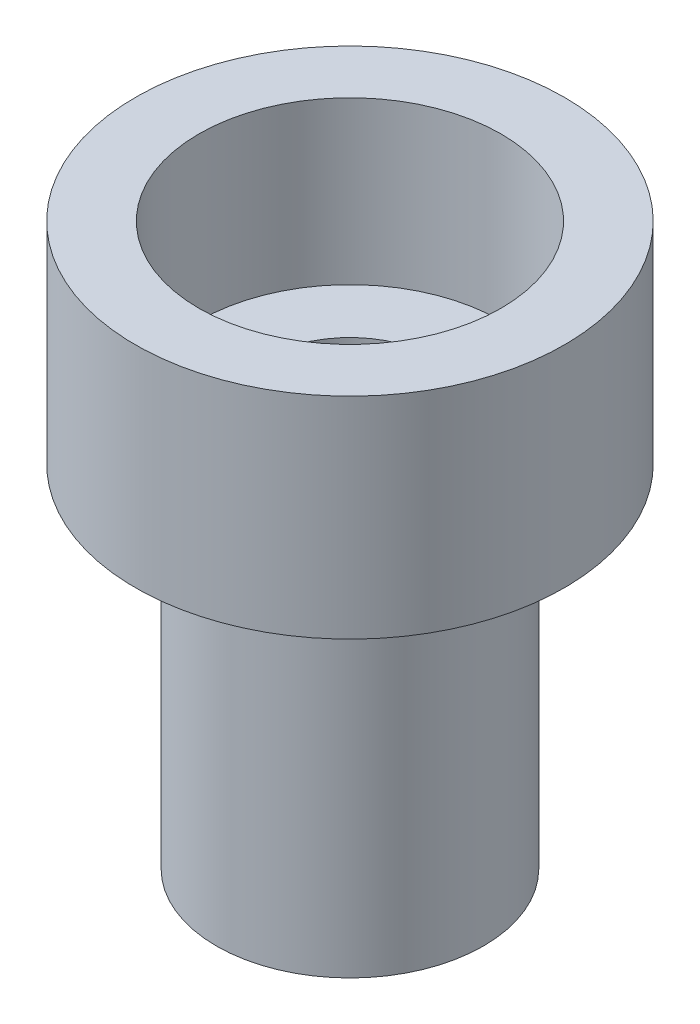
SolidWorks part; units mm, degrees
ref_plane "Front Plane" through (0, 0, 0) normal (0, 0, 1) x (1, 0, 0)
ref_plane "Top Plane" through (0, 0, 0) normal (0, 1, 0) x (1, 0, 0)
ref_plane "Right Plane" through (0, 0, 0) normal (1, 0, 0) x (0, 0, -1)
sketch "Sketch2" plane through (0, 0, 0) normal (0, 0, 1) x (1, 0, 0)
  line L0 (0, 0) -> (0, 7.3124) construction
  line L1 (2.8, 10.4) -> (2.8, 7.4)
  line L2 (2.8, 7.4) -> (1.6, 7.4)
  line L3 (1.6, 7.4) -> (1.6, 0)
  line L4 (1.6, 0) -> (2.475, 0)
  line L5 (2.475, 0) -> (2.475, 6.5)
  line L6 (2.475, 6.5) -> (3.975, 6.5)
  line L7 (3.975, 6.5) -> (3.975, 10.4)
  line L8 (3.975, 10.4) -> (2.8, 10.4)
  point P9 (3.3875, 10.4)
  point P12 (2.0375, 0)
  dimension "D1" = 3.975
  dimension "D2" = 2.8
  dimension "D3" = 3.9
  dimension "D4" = 3
  dimension "D5" = 2.475
  dimension "D6" = 1.6
  dimension "D7" = 10.4
revolve "Revolve1" add sketch "Sketch2" angle 360 about L0
